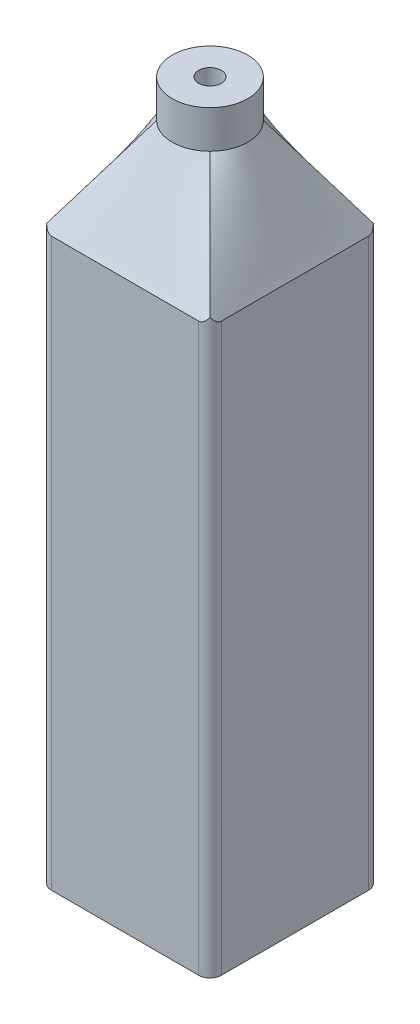
SolidWorks part; units mm, degrees
ref_plane "前视基准面" through (0, 0, 0) normal (0, 0, 1) x (1, 0, 0)
ref_plane "上视基准面" through (0, 0, 0) normal (0, 1, 0) x (1, 0, 0)
ref_plane "右视基准面" through (0, 0, 0) normal (1, 0, 0) x (0, 0, -1)
sketch "草图1" plane through (0, 0, 0) normal (0, 1, 0) x (1, 0, 0)
  line L1 (-22.5, 22.5) -> (22.5, 22.5)
  line L2 (-22.5, 22.5) -> (-22.5, -22.5)
  line L3 (-22.5, -22.5) -> (22.5, -22.5)
  line L4 (22.5, 22.5) -> (22.5, -22.5)
  line L5 (0, -22.5) -> (0, 22.5) construction
  line L6 (-22.5, 0) -> (22.5, 0) construction
  point P0 (0, 0)
  dimension "D1" = 45
  dimension "D2" = 45
extrude "凸台-拉伸1" add sketch "草图1" along normal blind 150
sketch "草图2" plane through (0, 150, 0) normal (0, 1, 0) x (1, 0, 0)
  line L4 (22.5, -22.5) -> (22.5, 22.5)
  line L5 (22.5, 22.5) -> (-22.5, 22.5)
  line L6 (-22.5, 22.5) -> (-22.5, -22.5)
  line L7 (-22.5, -22.5) -> (22.5, -22.5)
  line L8 (22.5, -22.5) -> (22.5, 22.5)
  line L9 (22.5, 22.5) -> (-22.5, 22.5)
  line L10 (-22.5, 22.5) -> (-22.5, -22.5)
  line L11 (-22.5, -22.5) -> (22.5, -22.5)
  dimension "D1" = 0
ref_plane "基准面1" through (0, 175, 0) normal (0, 1, 0) x (1, 0, 0)
sketch "草图3" plane through (0, 175, 0) normal (0, 1, 0) x (1, 0, 0)
  circle A0 centre (0, 0) radius 10
  dimension "D1" = 20
loft "放样1" add profiles "草图3", "草图2"
sketch "草图4" plane through (0, 175, 0) normal (0, 1, 0) x (1, 0, 0)
  arc A4 (-7.0711, 7.0711) -> (-7.0711, -7.0711) centre (0, 0) ccw
  arc A5 (-7.0711, -7.0711) -> (7.0711, -7.0711) centre (0, 0) ccw
  arc A6 (7.0711, -7.0711) -> (7.0711, 7.0711) centre (0, 0) ccw
  arc A7 (7.0711, 7.0711) -> (-7.0711, 7.0711) centre (0, 0) ccw
  arc A8 (-7.0711, 7.0711) -> (-7.0711, -7.0711) centre (0, 0) ccw
  arc A9 (-7.0711, -7.0711) -> (7.0711, -7.0711) centre (0, 0) ccw
  arc A10 (7.0711, -7.0711) -> (7.0711, 7.0711) centre (0, 0) ccw
  arc A11 (7.0711, 7.0711) -> (-7.0711, 7.0711) centre (0, 0) ccw
  dimension "D1" = 0
extrude "凸台-拉伸2" add sketch "草图4" along normal blind 10
sketch "草图5" plane through (0, 185, 0) normal (0, 1, 0) x (1, 0, 0)
  circle A0 centre (0, 0) radius 3
  dimension "D1" = 6
extrude "切除-拉伸1" cut sketch "草图5" against normal blind 30
fillet "圆角1" radius 3 4 edges at (22.5, 75, -22.5) (22.5, 75, 22.5) (-22.5, 75, -22.5) (-22.5, 75, 22.5)
